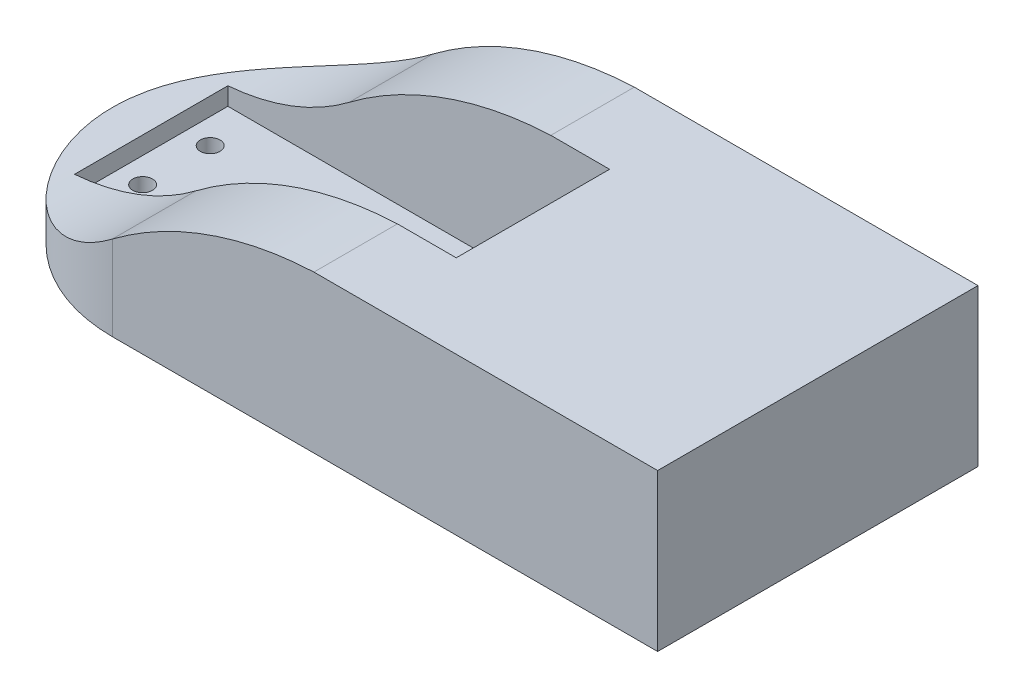
SolidWorks part; units mm, degrees
ref_plane "Front Plane" through (0, 0, 0) normal (0, 0, 1) x (1, 0, 0)
ref_plane "Top Plane" through (0, 0, 0) normal (0, 1, 0) x (1, 0, 0)
ref_plane "Right Plane" through (0, 0, 0) normal (1, 0, 0) x (0, 0, -1)
sketch "Sketch1" plane through (0, 0, 0) normal (0, 1, 0) x (1, 0, 0)
  line L0 (38.2, -11.25) -> (-17.8, -11.25)
  line L1 (0, 23.5) -> (80, 23.5)
  line L2 (0, 23.5) -> (0, -23.5)
  line L3 (0, -23.5) -> (80, -23.5)
  line L4 (80, 23.5) -> (80, -23.5)
  line L5 (-17.8, -11.25) -> (-17.8, 11.25)
  line L6 (-17.8, 11.25) -> (38.2, 11.25)
  line L7 (38.2, 11.25) -> (38.2, -11.25)
  circle A0 centre (0, 0) radius 23.5
  point P11 (0, 0)
  line B0 (-17.3, 2.3) -> (-17.3, 0.8)
  line B1 (-17.3, 0.75) -> (-17.3, -0.75)
  line B2 (11.8, -8.9) -> (11.8, -2)
  line B3 (11.8, 2) -> (11.8, 8.9)
  line B4 (11.8, 8.9) -> (3.9815, 8.9)
  line B5 (3.9815, -8.9) -> (11.8, -8.9)
  line B6 (24.5, 8.9) -> (24.5, 5.1324)
  line B7 (24.5, -5.1324) -> (24.5, -8.9)
  line B8 (24.5, -8.9) -> (3.9815, -8.9)
  line B9 (0, -9.75) -> (29.7, -9.75)
  line B10 (29.7, -9.75) -> (29.7, 9.75)
  line B11 (29.7, 9.75) -> (0, 9.75)
  line B12 (3.9815, 8.9) -> (24.5, 8.9)
  line B13 (23.4, -7.85) -> (23.4, 7.85)
  line B14 (23.4, 7.85) -> (12.9, 7.85)
  line B15 (12.9, 7.85) -> (12.9, -7.85)
  line B16 (12.9, -7.85) -> (23.4, -7.85)
  line B17 (24.5, -8.9) -> (24.5, 8.9)
  line B18 (24.5, 8.9) -> (11.8, 8.9)
  line B19 (11.8, 8.9) -> (11.8, -8.9)
  line B20 (11.8, -8.9) -> (24.5, -8.9)
  line B21 (24.5, 5.1324) -> (24.5, -5.1324)
  line B22 (11.8, -2) -> (11.8, 2)
  line B23 (-9.8, 0.5) -> (-16.8, 0.5)
  line B24 (-16.8, 0.5) -> (-16.8, -0.5)
  line B25 (-16.8, -0.5) -> (-9.8, -0.5)
  line B26 (-9.8, -0.5) -> (-9.8, 0.5)
  line B27 (-9.8, -0.5) -> (-16.8, -0.5)
  line B28 (-16.8, -0.5) -> (-16.8, -3.45)
  line B29 (-16.3, -3.95) -> (-15.8321, -3.95)
  line B30 (-15.8321, -5.95) -> (-16.3, -5.95)
  line B31 (-16.8, -6.45) -> (-16.8, -7.75)
  line B32 (-15.3, -9.25) -> (-9.8, -9.25)
  line B33 (-9.8, -9.25) -> (-9.8, -0.5)
  line B34 (-16.8, 0.5) -> (-9.8, 0.5)
  line B35 (-9.8, 0.5) -> (-9.8, 9.25)
  line B36 (-9.8, 9.25) -> (-15.3, 9.25)
  line B37 (-16.8, 7.75) -> (-16.8, 6.45)
  line B38 (-16.3, 5.95) -> (-15.8321, 5.95)
  line B39 (-15.8321, 3.95) -> (-16.3, 3.95)
  line B40 (-16.8, 3.45) -> (-16.8, 0.5)
  line B41 (23.4, -7.85) -> (23.4, 7.85)
  line B42 (37.2, 0.5) -> (30.2, 0.5)
  line B43 (30.2, 0.5) -> (30.2, -0.5)
  line B44 (30.2, -0.5) -> (37.2, -0.5)
  line B45 (37.2, -0.5) -> (37.2, 0.5)
  line B46 (-16.8, 0.5) -> (-9.8, 0.5)
  line B47 (-9.8, 0.5) -> (-9.8, 9.25)
  line B48 (-9.8, 9.25) -> (-15.3, 9.25)
  line B49 (-16.8, 7.75) -> (-16.8, 6.45)
  line B50 (-16.3, 5.95) -> (-15.8321, 5.95)
  line B51 (-15.8321, 3.95) -> (-16.3, 3.95)
  line B52 (-16.8, 3.45) -> (-16.8, 0.5)
  line B53 (-9.8, -0.5) -> (-16.8, -0.5)
  line B54 (-16.8, -0.5) -> (-16.8, -3.45)
  line B55 (-16.3, -3.95) -> (-15.8321, -3.95)
  line B56 (-15.8321, -5.95) -> (-16.3, -5.95)
  line B57 (-16.8, -6.45) -> (-16.8, -7.75)
  line B58 (-15.3, -9.25) -> (-9.8, -9.25)
  line B59 (-9.8, -9.25) -> (-9.8, -0.5)
  line B60 (37.2, -0.5) -> (30.2, -0.5)
  line B61 (30.2, -0.5) -> (30.2, -9.25)
  line B62 (30.2, -9.25) -> (35.7, -9.25)
  line B63 (37.2, -7.75) -> (37.2, -6.45)
  line B64 (36.7, -5.95) -> (36.2321, -5.95)
  line B65 (36.2321, -3.95) -> (36.7, -3.95)
  line B66 (37.2, -3.45) -> (37.2, -0.5)
  line B67 (30.2, 9.25) -> (30.2, 0.5)
  line B68 (30.2, 0.5) -> (37.2, 0.5)
  line B69 (37.2, 0.5) -> (37.2, 3.45)
  line B70 (36.7, 3.95) -> (36.2321, 3.95)
  line B71 (36.2321, 5.95) -> (36.7, 5.95)
  line B72 (37.2, 6.45) -> (37.2, 7.75)
  line B73 (35.7, 9.25) -> (30.2, 9.25)
  line B74 (-9.8, 9.5) -> (-9.8, -9.5)
  line B75 (-9.3, -10) -> (29.7, -10)
  line B76 (30.2, -9.5) -> (30.2, 9.5)
  line B77 (29.7, 10) -> (-9.3, 10)
  line B78 (0, 9.75) -> (-9.3, 9.75)
  line B79 (-9.3, 9.75) -> (-9.3, 2.9279)
  line B80 (-9.3, -2.9279) -> (-9.3, -9.75)
  line B81 (-9.3, -9.75) -> (0, -9.75)
  line B82 (-14.3, 3.2203) -> (-14.3, 2.921)
  line B83 (-14.3, 2.921) -> (-10.3, 3.2007)
  line B84 (-10.3, 3.2887) -> (-10.3, 3.2007)
  line B85 (-10.1143, 3.5) -> (-10.3, 3.5)
  line B86 (-10.3, 3.5) -> (-14.3, 3.2203)
  line B87 (-14.3, -2.921) -> (-14.3, -3.2203)
  line B88 (-14.3, -3.2203) -> (-10.3, -3.5)
  line B89 (-10.3, -3.5) -> (-10.1143, -3.5)
  line B90 (-10.3, -3.2007) -> (-10.3, -3.2887)
  line B91 (-10.3, -3.2007) -> (-14.3, -2.921)
  line B92 (-10.3, -9.25) -> (-10.3, -9.75)
  line B93 (-9.8, -10.25) -> (30.2, -10.25)
  line B94 (30.7, -9.75) -> (30.7, -9.25)
  line B95 (30.7, -9.25) -> (30.2, -9.25)
  line B96 (30.2, -9.25) -> (30.2, -9.5)
  line B97 (29.7, -10) -> (-9.3, -10)
  line B98 (-9.8, -9.5) -> (-9.8, -9.25)
  line B99 (-9.8, -9.25) -> (-10.3, -9.25)
  line B100 (30.2, 10.25) -> (-9.8, 10.25)
  line B101 (-10.3, 9.75) -> (-10.3, 9.25)
  line B102 (-10.3, 9.25) -> (-9.8, 9.25)
  line B103 (-9.8, 9.25) -> (-9.8, 9.5)
  line B104 (-9.3, 10) -> (29.7, 10)
  line B105 (30.2, 9.5) -> (30.2, 9.25)
  line B106 (30.2, 9.25) -> (30.7, 9.25)
  line B107 (30.7, 9.25) -> (30.7, 9.75)
  line B108 (-17.3, 2.3) -> (-16.8, 2.3)
  line B109 (-17.3, 2.3) -> (-17.3, -2.301)
  line B110 (-17.3, -2.301) -> (-16.8, -2.301)
  line B111 (-16.8, 2.3) -> (-16.8, -2.301)
  circle B112 centre (0, 0) radius 5.3
  arc B113 (11.8, 2) -> (11.8, -2) centre (11.8, 0) ccw
  arc B114 (3.9815, 8.9) -> (3.9815, -8.9) centre (0, 0) ccw
  arc B115 (24.5, -5.1324) -> (24.5, 5.1324) centre (20.8069, 0) ccw
  arc B116 (0, -9.75) -> (3.9815, -8.9) centre (0, 0) ccw
  arc B117 (3.9815, 8.9) -> (0, 9.75) centre (0, 0) ccw
  arc B118 (24.5, -5.1324) -> (24.5, 5.1324) centre (20.8069, 0) ccw
  arc B119 (11.8, 2) -> (11.8, -2) centre (11.8, 0) ccw
  arc B120 (-16.8, -3.45) -> (-16.3, -3.95) centre (-16.3, -3.45) ccw
  arc B121 (-15.8321, -5.95) -> (-15.8321, -3.95) centre (-14.1, -4.95) ccw
  arc B122 (-16.3, -5.95) -> (-16.8, -6.45) centre (-16.3, -6.45) ccw
  arc B123 (-16.8, -7.75) -> (-15.3, -9.25) centre (-15.3, -7.75) ccw
  arc B124 (-15.3, 9.25) -> (-16.8, 7.75) centre (-15.3, 7.75) ccw
  arc B125 (-16.8, 6.45) -> (-16.3, 5.95) centre (-16.3, 6.45) ccw
  arc B126 (-15.8321, 3.95) -> (-15.8321, 5.95) centre (-14.1, 4.95) ccw
  arc B127 (-16.3, 3.95) -> (-16.8, 3.45) centre (-16.3, 3.45) ccw
  circle B128 centre (0, 0) radius 3
  circle B129 centre (0, 0) radius 6.5
  arc B130 (-15.3, 9.25) -> (-16.8, 7.75) centre (-15.3, 7.75) ccw
  arc B131 (-16.8, 6.45) -> (-16.3, 5.95) centre (-16.3, 6.45) ccw
  arc B132 (-15.8321, 3.95) -> (-15.8321, 5.95) centre (-14.1, 4.95) ccw
  arc B133 (-16.3, 3.95) -> (-16.8, 3.45) centre (-16.3, 3.45) ccw
  arc B134 (-16.8, -3.45) -> (-16.3, -3.95) centre (-16.3, -3.45) ccw
  arc B135 (-15.8321, -5.95) -> (-15.8321, -3.95) centre (-14.1, -4.95) ccw
  arc B136 (-16.3, -5.95) -> (-16.8, -6.45) centre (-16.3, -6.45) ccw
  arc B137 (-16.8, -7.75) -> (-15.3, -9.25) centre (-15.3, -7.75) ccw
  arc B138 (35.7, -9.25) -> (37.2, -7.75) centre (35.7, -7.75) ccw
  arc B139 (37.2, -6.45) -> (36.7, -5.95) centre (36.7, -6.45) ccw
  arc B140 (36.2321, -3.95) -> (36.2321, -5.95) centre (34.5, -4.95) ccw
  arc B141 (36.7, -3.95) -> (37.2, -3.45) centre (36.7, -3.45) ccw
  arc B142 (37.2, 3.45) -> (36.7, 3.95) centre (36.7, 3.45) ccw
  arc B143 (36.2321, 5.95) -> (36.2321, 3.95) centre (34.5, 4.95) ccw
  arc B144 (36.7, 5.95) -> (37.2, 6.45) centre (36.7, 6.45) ccw
  arc B145 (37.2, 7.75) -> (35.7, 9.25) centre (35.7, 7.75) ccw
  arc B146 (-9.8, -9.5) -> (-9.3, -10) centre (-9.3, -9.5) ccw
  arc B147 (29.7, -10) -> (30.2, -9.5) centre (29.7, -9.5) ccw
  arc B148 (30.2, 9.5) -> (29.7, 10) centre (29.7, 9.5) ccw
  arc B149 (-9.3, 10) -> (-9.8, 9.5) centre (-9.3, 9.5) ccw
  arc B150 (0, 9.75) -> (-9.3, 2.9279) centre (0, 0) ccw
  arc B151 (-9.3, -2.9279) -> (0, -9.75) centre (0, 0) ccw
  arc B152 (-10.3, -9.75) -> (-9.8, -10.25) centre (-9.8, -9.75) ccw
  arc B153 (30.2, -10.25) -> (30.7, -9.75) centre (30.2, -9.75) ccw
  arc B154 (29.7, -10) -> (30.2, -9.5) centre (29.7, -9.5) ccw
  arc B155 (-9.8, -9.5) -> (-9.3, -10) centre (-9.3, -9.5) ccw
  arc B156 (-9.8, 10.25) -> (-10.3, 9.75) centre (-9.8, 9.75) ccw
  arc B157 (-9.3, 10) -> (-9.8, 9.5) centre (-9.3, 9.5) ccw
  arc B158 (30.2, 9.5) -> (29.7, 10) centre (29.7, 9.5) ccw
  arc B159 (30.7, 9.75) -> (30.2, 10.25) centre (30.2, 9.75) ccw
  ellipse B160 centre (-10.0312, 3.2181) end of major axis (-9.9246, 3.5032) minor radius 0.2777 (-10.1143, 3.5) -> (-10.3, 3.2887) ccw
  ellipse B161 centre (-10.0312, -3.2181) end of major axis (-9.9246, -3.5032) minor radius 0.2777 (-10.3, -3.2887) -> (-10.1143, -3.5) ccw
  dimension "D1" = 47
  dimension "D2" = 80
sketch_block_instance "MG996R_TOP-1"
sketch_block "MG996R_TOP"
extrude "Boss-Extrude1" add sketch "Sketch1" along normal blind 23 contours A0 | L3 L4 L1 L2
sketch "Sketch3" plane through (0, 23, 0) normal (0, 1, 0) x (1, 0, 0)
  line L0 (38.2, 11.25) -> (38.2, -11.25) construction
  line L1 (38.2, -11.25) -> (-17.8, -11.25) construction
  line L2 (-17.8, 11.25) -> (38.2, 11.25) construction
  line L3 (-17.8, -11.25) -> (-17.8, 11.25) construction
  line L4 (38.2, 11.25) -> (38.2, -11.25)
  line L5 (38.2, -11.25) -> (-17.8, -11.25)
  line L6 (-17.8, 11.25) -> (38.2, 11.25)
  line L7 (-17.8, -11.25) -> (-17.8, 11.25)
extrude "Cut-Extrude1" cut sketch "Sketch3" against normal offset from surface (20 mm away) 3 up to face at (34.125, 0, 0)
sketch "Sketch4" plane through (0, 0, 23.5) normal (0, 0, 1) x (1, 0, 0)
  line L0 (0, 23) -> (80, 23) construction
  line L1 (0, 23) -> (-23.5, 23) construction
  line L2 (-17.8, 23) -> (38.2, 23) construction
  line L3 (0, 23) -> (29.5742, 23)
  line L4 (0, 23) -> (-23.5, 23)
  line L5 (-17.8, 23) -> (29.5742, 23)
  line L14 (-23.5, 23) -> (-23.5, 0) construction
  line L15 (-23.5, 23) -> (-23.5, 5.6342)
  arc A2 (-23.5, 5.6342) -> (0, 12.4092) centre (-20.5228, 39.4514) ccw
  arc A3 (0, 12.4092) -> (29.5742, 23) centre (31.7759, -29.7356) cw
  point P6 (0, 12.4092)
  point P8 (40, 23)
  point P9 (0, 0)
  point P10 (28.8083, 22.5724)
  point P16 (0, 0)
  point P17 (40, 23)
  point P18 (29.5742, 23)
extrude "Cut-Extrude2" cut sketch "Sketch4" against normal through all contours L3 L4 L15 A2 A3
sketch "Sketch6" plane through (0, 3, 0) normal (0, 1, 0) x (1, 0, 0)
  point P0 (-14.1004, 4.9532)
  point P1 (-14.1004, -4.9563)
  point P2 (34.5, -4.95)
  point P3 (34.5, 4.9532)
hole_wizard "M3.5x0.6 Tapped Hole1" positions "Sketch6" profile "Sketch7" tap size "M3.5x0.6" standard "ANSI Metric" end condition through all
sketch "Sketch7" plane through (-14.1004, 3, -4.9532) normal (1, 0, 0) x (0, 0, 1)
  line L0 (0, 0) -> (0, 3)
  line L1 (0, 3) -> (1.45, 3)
  line L2 (1.45, 3) -> (1.45, 0)
  line L5 (1.45, 0) -> (0, 0)
  line L11 (0, -6.35) -> (0, 107.95) construction
  dimension "Thru Tap Drill Dia." = 2.9
  dimension "Thru Tap Drill Depth" = 3
cosmetic thread "Hole Thread1" parameters "D2"=3.5
cosmetic thread "Hole Thread2" parameters "D2"=3.5
cosmetic thread "Hole Thread3" parameters "D2"=3.5
cosmetic thread "Hole Thread4" parameters "D2"=3.5
